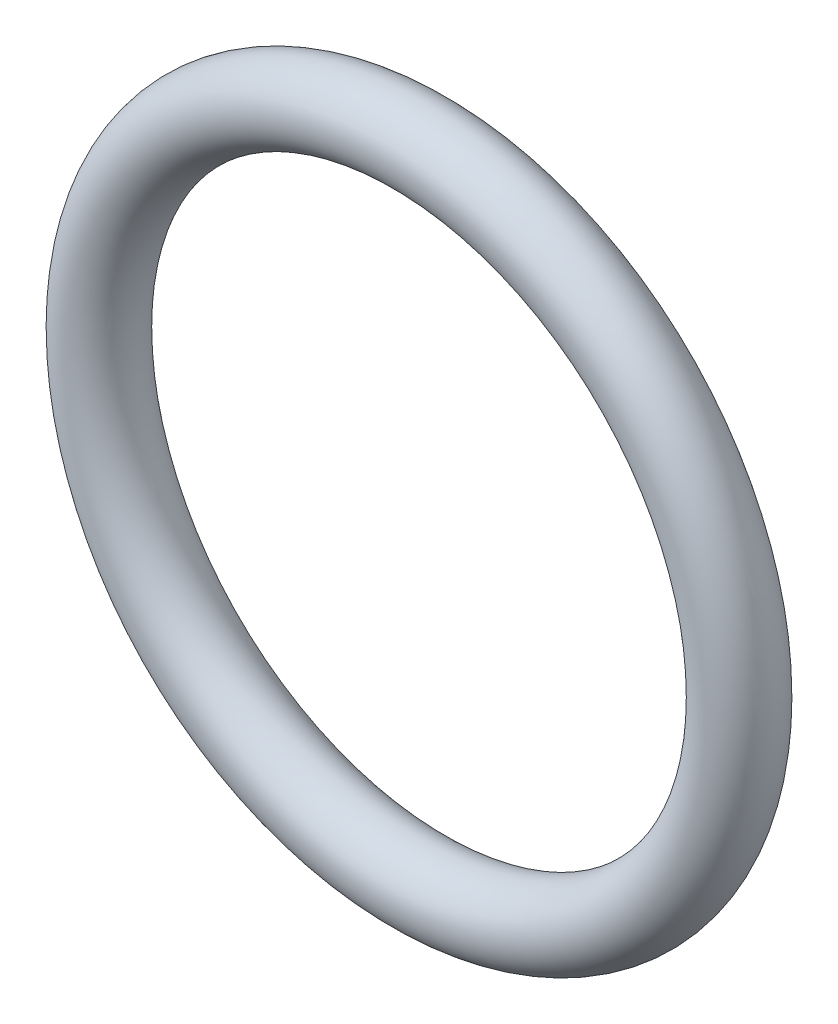
SolidWorks part; units mm, degrees
ref_plane "Face" through (0, 0, 0) normal (0, 0, 1) x (1, 0, 0)
ref_plane "Dessus" through (0, 0, 0) normal (0, 1, 0) x (1, 0, 0)
ref_plane "Droite" through (0, 0, 0) normal (1, 0, 0) x (0, 0, -1)
sketch "Esquisse1" plane through (0, 0, 0) normal (0, 1, 0) x (1, 0, 0)
  line L0 (0, 0) -> (0, 53.3279) construction
  line L1 (-72.6804, 0) -> (66.3713, 0) construction
  circle A0 centre (-15, 0) radius 1.75
  dimension "D1" = 3.5
  dimension "D2" = 15
revolve "Révolution1" add sketch "Esquisse1" angle 360 about L0
